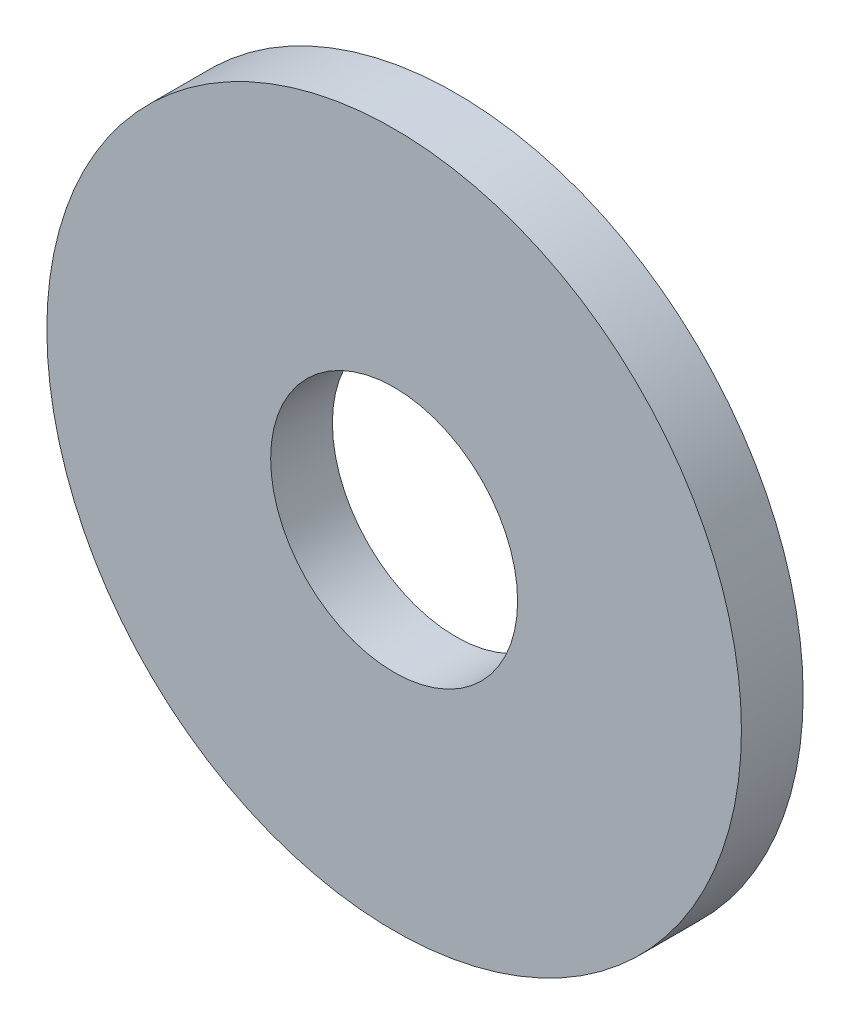
SolidWorks part; units mm, degrees
ref_plane "前视基准面" through (0, 0, 0) normal (0, 0, 1) x (1, 0, 0)
ref_plane "上视基准面" through (0, 0, 0) normal (0, 1, 0) x (1, 0, 0)
ref_plane "右视基准面" through (0, 0, 0) normal (1, 0, 0) x (0, 0, -1)
sketch "草图1" plane through (0, 0, 0) normal (0, 0, 1) x (1, 0, 0)
  circle A0 centre (0, 0) radius 1.6
  circle A1 centre (0, 0) radius 4.5
  dimension "D1" = 3.2
  dimension "D2" = 9
extrude "凸台-拉伸1" add sketch "草图1" along normal blind 0.8
